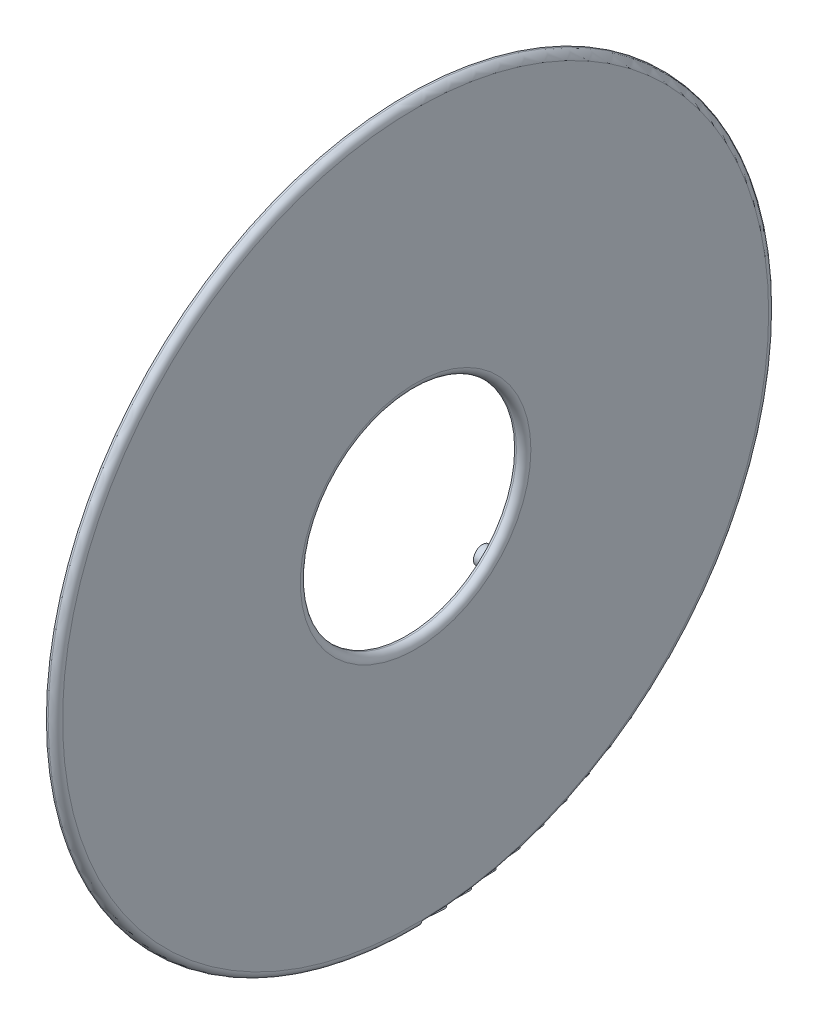
SolidWorks part; units mm, degrees
ref_plane "Front Plane" through (0, 0, 0) normal (0, 0, 1) x (1, 0, 0)
ref_plane "Top Plane" through (0, 0, 0) normal (0, 1, 0) x (1, 0, 0)
ref_plane "Right Plane" through (0, 0, 0) normal (1, 0, 0) x (0, 0, -1)
sketch "Sketch1" plane through (0, 0, 0) normal (1, 0, 0) x (0, 0, -1)
  circle A0 centre (0, 0) radius 7.62
  circle A1 centre (0, 0) radius 25.4
  dimension "D1" = 15.24
  dimension "D2" = 50.8
extrude "Boss-Extrude1" add sketch "Sketch1" along normal blind 0.635
fillet "Fillet1" radius 0.508 2 edges at (0.635, 0, -7.62) (0.635, 0, -25.4)
sketch "Sketch2" plane through (0, 0, 0) normal (-1, 0, 0) x (0, 0, 1)
  line L0 (0, 10.795) -> (0, 0) construction
  line L1 (0, 0) -> (-7.6332, 7.6332) construction
  circle A0 centre (0, 0) radius 10.795 construction
  circle A1 centre (-7.6332, 7.6332) radius 0.635
  circle A2 centre (7.6332, 7.6332) radius 0.635
  circle A3 centre (7.6332, -7.6332) radius 0.635
  circle A4 centre (-7.6332, -7.6332) radius 0.635
  point P15 (0, 0)
  dimension "D1" = 21.59
  dimension "D2" = 1.27
  dimension "D3" = 45
  dimension "D4" = 4
extrude "Boss-Extrude2" add sketch "Sketch2" along normal blind 2.286
